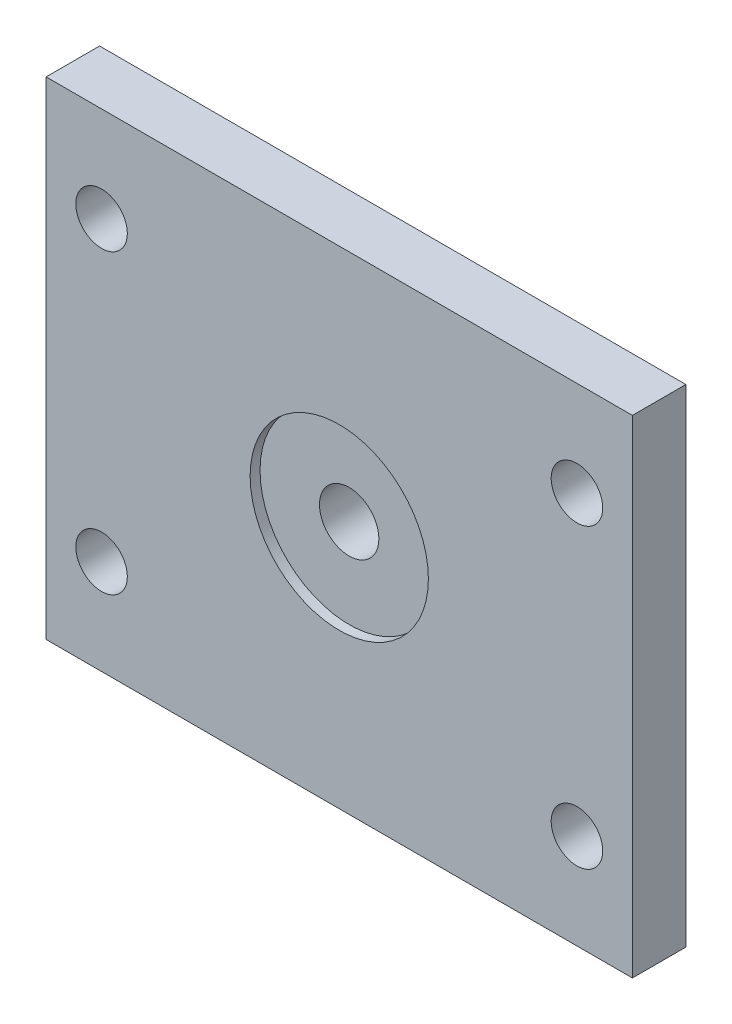
SolidWorks part; units mm, degrees
ref_plane "Front Plane" through (0, 0, 0) normal (0, 0, 1) x (1, 0, 0)
ref_plane "Top Plane" through (0, 0, 0) normal (0, 1, 0) x (1, 0, 0)
ref_plane "Right Plane" through (0, 0, 0) normal (1, 0, 0) x (0, 0, -1)
sketch "Sketch1" plane through (0, 0, 0) normal (0, 0, 1) x (1, 0, 0)
  line L1 (148, -123) -> (-148, -123)
  line L2 (148, -123) -> (148, 123)
  line L3 (148, 123) -> (-148, 123)
  line L4 (-148, -123) -> (-148, 123)
  line L5 (148, -123) -> (-148, 123) construction
  line L6 (148, 123) -> (-148, -123) construction
  circle A0 centre (120, -75) radius 13 construction
  circle A1 centre (-120, -75) radius 13 construction
  circle A2 centre (-120, 75) radius 13 construction
  circle A3 centre (120, 75) radius 13 construction
  circle A4 centre (-120, 75) radius 13
  circle A5 centre (120, 75) radius 13
  circle A6 centre (120, -75) radius 13
  circle A7 centre (-120, -75) radius 13
  point P0 (0, 0)
  dimension "D1" = 296
  dimension "D2" = 246
extrude "Extrude1" add sketch "Sketch1" along normal blind 27
sketch "Sketch2" plane through (0, 0, 27) normal (0, 0, -1) x (-1, 0, 0)
  circle A0 centre (0, 0) radius 45
  dimension "D1" = 90
extrude "Extrude2" cut sketch "Sketch2" along normal blind 5
sketch "Sketch3" plane through (0, 0, 22) normal (0, 0, 1) x (1, 0, 0)
  circle A0 centre (0, 0) radius 15
  dimension "D1" = 30
extrude "Extrude3" cut sketch "Sketch3" against normal through all
